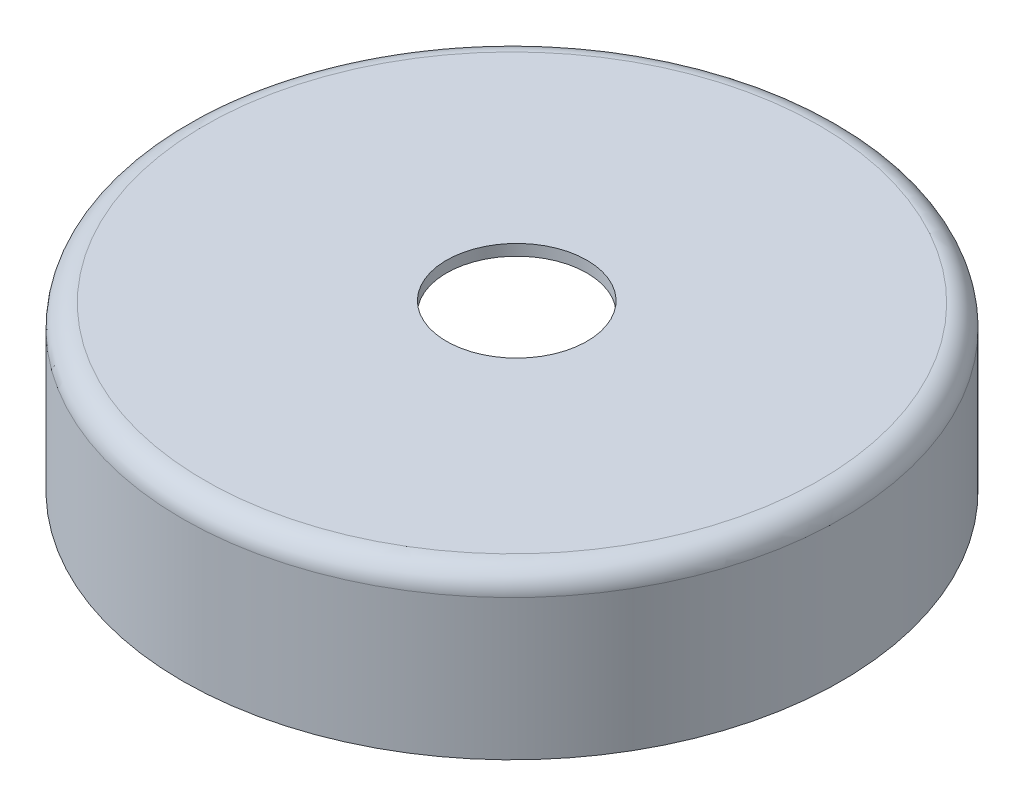
SolidWorks part; units mm, degrees
material "PVC Rigid"
ref_plane "Front" through (0, 0, 0) normal (0, 0, 1) x (1, 0, 0)
ref_plane "Top" through (0, 0, 0) normal (0, 1, 0) x (1, 0, 0)
ref_plane "Right" through (0, 0, 0) normal (1, 0, 0) x (0, 0, -1)
sketch "Sketch1" plane through (0, 0, 0) normal (1, 0, 0) x (0, 0, -1)
  line L0 (-136.525, 0) -> (136.525, 0) construction
  line L1 (-136.525, 0) -> (-136.7234, 0) construction
  line L2 (-136.7234, 0) -> (-141.4859, 0) construction
  line L3 (136.525, 0) -> (136.7234, 0) construction
  line L4 (136.7234, 0) -> (141.4859, 0) construction
  line L5 (0, 0) -> (0, 69.85)
  line L6 (-141.4859, 0) -> (-141.4859, 69.85)
  line L7 (-141.4859, 69.85) -> (141.4859, 69.85) construction
  line L8 (141.4859, 69.85) -> (141.4859, 0) construction
  line L9 (-141.4859, 69.85) -> (0, 69.85)
  line L10 (0, 0) -> (-141.4859, 0)
  dimension "D2" = 0.1984
revolve "Revolve1" add sketch "Sketch1" angle 360 about L5
fillet "Fillet1" radius 9.525 1 edges at (0, 69.85, -141.4859)
shell "Shell1" thickness 4.7625
sketch "Sketch3" plane through (0, 69.85, 0) normal (0, 1, 0) x (1, 0, 0)
  circle A1 centre (0.2189, 1.8107) radius 30.1625
extrude "Cut-Extrude1" cut sketch "Sketch3" against normal blind 28.194 and the other way blind 30.734
equation "\"D1@Shell1\" = \"Wall Thickness@Sketch1\""
